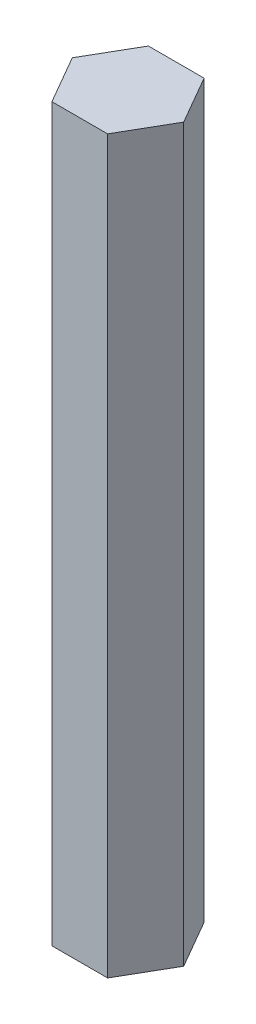
SolidWorks part; units mm, degrees
ref_plane "Front Plane" through (0, 0, 0) normal (0, 0, 1) x (1, 0, 0)
ref_plane "Top Plane" through (0, 0, 0) normal (0, 1, 0) x (1, 0, 0)
ref_plane "Right Plane" through (0, 0, 0) normal (1, 0, 0) x (0, 0, -1)
sketch "Sketch1" plane through (0, 0, 0) normal (0, 1, 0) x (1, 0, 0)
  line L1 (7.9771, 1.5793) -> (3.9771, 8.5075)
  line L2 (3.9771, 8.5075) -> (-4.0229, 8.5075)
  line L3 (-4.0229, 8.5075) -> (-8.0229, 1.5793)
  line L4 (-8.0229, 1.5793) -> (-4.0229, -5.3489)
  line L5 (-4.0229, -5.3489) -> (3.9771, -5.3489)
  line L6 (3.9771, -5.3489) -> (7.9771, 1.5793)
  circle A0 centre (-0.0229, 1.5793) radius 6.9282 construction
  dimension "D1" = 8
extrude "Boss-Extrude1" add sketch "Sketch1" along normal blind 105
